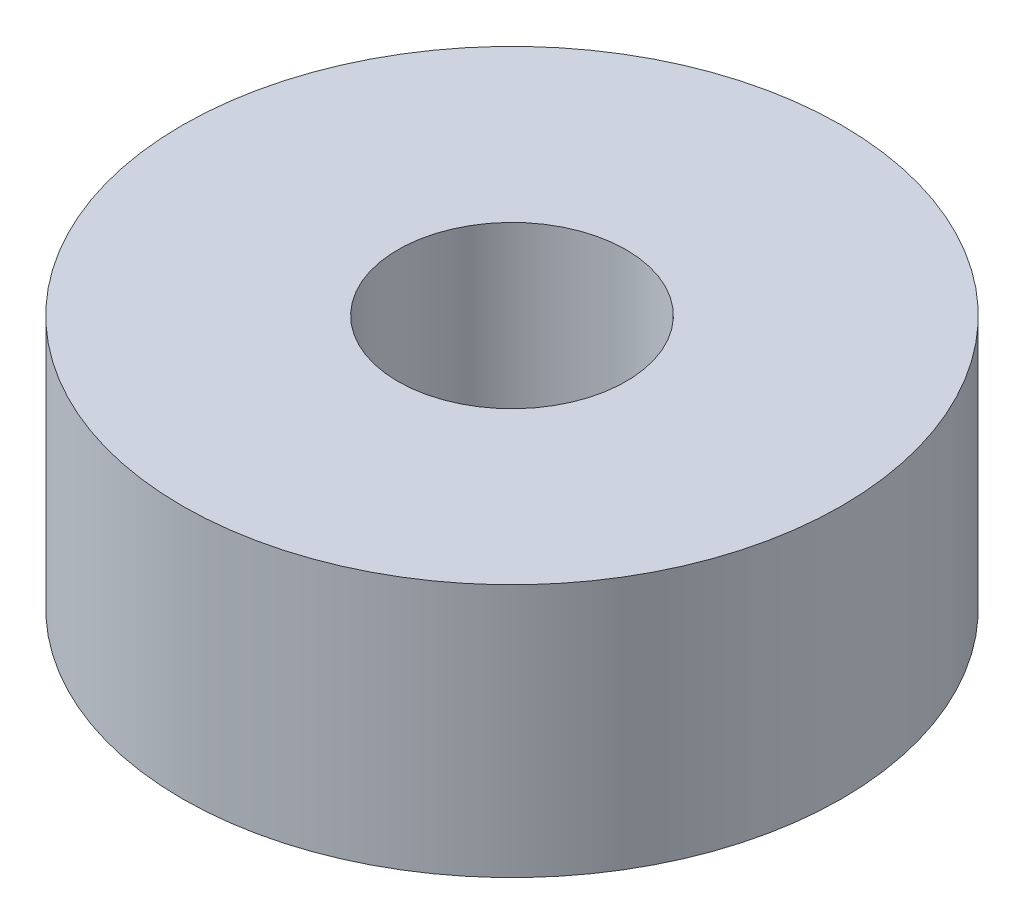
SolidWorks part; units mm, degrees
ref_plane "Front Plane" through (0, 0, 0) normal (0, 0, 1) x (1, 0, 0)
ref_plane "Top Plane" through (0, 0, 0) normal (0, 1, 0) x (1, 0, 0)
ref_plane "Right Plane" through (0, 0, 0) normal (1, 0, 0) x (0, 0, -1)
sketch "Sketch1" plane through (0, 0, 0) normal (0, 1, 0) x (1, 0, 0)
  circle A0 centre (0, 0) radius 6.5
  circle A1 centre (0, 0) radius 2.25
  dimension "D1" = 13
  dimension "D2" = 4.5
extrude "Boss-Extrude1" add sketch "Sketch1" along normal blind 5
